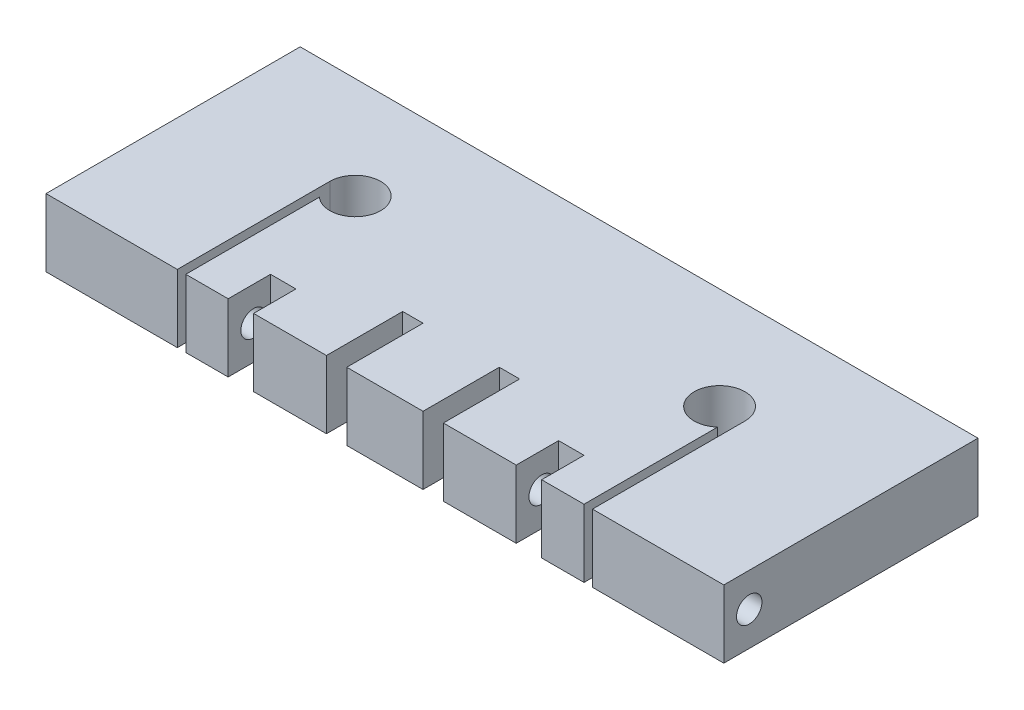
SolidWorks part; units mm, degrees
ref_plane "前视基准面" through (0, 0, 0) normal (0, 0, 1) x (1, 0, 0)
ref_plane "上视基准面" through (0, 0, 0) normal (0, 1, 0) x (1, 0, 0)
ref_plane "右视基准面" through (0, 0, 0) normal (1, 0, 0) x (0, 0, -1)
sketch "草图1" plane through (0, 0, 0) normal (0, 1, 0) x (1, 0, 0)
  line L1 (-40, -15) -> (40, -15)
  line L2 (-40, -15) -> (-40, 15)
  line L3 (-40, 15) -> (40, 15)
  line L4 (40, -15) -> (40, 15)
  line L5 (-40, -15) -> (40, 15) construction
  line L6 (-40, 15) -> (40, -15) construction
  point P0 (0, 0)
  dimension "D1" = 80
  dimension "D2" = 30
extrude "凸台-拉伸1" add sketch "草图1" along normal blind 8
sketch "草图2" plane through (0, 8, 0) normal (0, 1, 0) x (1, 0, 0)
  line L0 (0, 27.7349) -> (0, -22.8781) construction
  line L1 (-24.5, 3) -> (-24.5, -15)
  line L2 (-40, -15) -> (40, -15) construction
  line L3 (-24.5, -15) -> (-23.5, -15)
  line L4 (-23.5, -15) -> (-23.5, 0.7639)
  line L5 (23.5, -15) -> (23.5, 0.7639) construction
  line L6 (24.5, -15) -> (23.5, -15) construction
  line L7 (24.5, 3) -> (24.5, -15) construction
  line L8 (23.5, -15) -> (23.5, 0.7639)
  line L9 (24.5, -15) -> (23.5, -15)
  line L10 (24.5, 3) -> (24.5, -15)
  line L11 (40, 15) -> (-40, 15) construction
  arc A0 (-23.5, 0.7639) -> (-24.5, 3) centre (-21.5, 3) ccw
  arc A1 (23.5, 0.7639) -> (24.5, 3) centre (21.5, 3) cw construction
  arc A2 (-24.5, 3) -> (-23.5, 0.7639) centre (-21.5, 3) ccw construction
  arc A3 (23.5, 0.7639) -> (24.5, 3) centre (21.5, 3) cw construction
  arc A4 (24.5, 3) -> (23.5, 0.7639) centre (21.5, 3) cw construction
  arc A5 (23.5, 0.7639) -> (24.5, 3) centre (21.5, 3) cw
  dimension "D1" = 43
  dimension "D2" = 6
  dimension "D3" = 1
  dimension "D4" = 12
extrude "切除-拉伸1" cut sketch "草图2" against normal through all
sketch "草图3" plane through (0, 8, 0) normal (0, 1, 0) x (1, 0, 0)
  line L0 (0, 25.2639) -> (0, -30.4616) construction
  line L1 (-40, -15) -> (-24.5, -15) construction
  line L2 (-4.5, -15) -> (-6.9, -15)
  line L3 (-4.5, -15) -> (-4.5, -6)
  line L4 (-4.5, -6) -> (-6.9, -6)
  line L5 (-6.9, -15) -> (-6.9, -6)
  line L6 (4.5, -6) -> (6.9, -6)
  line L7 (6.9, -15) -> (6.9, -6)
  line L8 (4.5, -15) -> (6.9, -15)
  line L9 (4.5, -15) -> (4.5, -6)
  dimension "D1" = 9
  dimension "D2" = 2.4
  dimension "D3" = 9
extrude "切除-拉伸2" cut sketch "草图3" against normal through all and the other way through all
sketch "草图5" plane through (-40, 0, 0) normal (-1, 0, 0) x (0, 0, 1)
  line L0 (-15, 8) -> (15, 8) construction
  line L2 (15, 8) -> (15, 0) construction
  circle A0 centre (12, 4) radius 1.5
  dimension "D1" = 3
  dimension "D2" = 4
  dimension "D3" = 3
extrude "切除-拉伸3" cut sketch "草图5" against normal blind 32
sketch "草图6" plane through (0, 0, 15) normal (0, 0, 1) x (1, 0, 0)
  line L0 (-23.5, 8) -> (-6.9, 8) construction
  line L1 (-18.5, 8) -> (-15.5, 8)
  line L2 (-18.5, 8) -> (-18.5, 0)
  line L3 (-18.5, 0) -> (-15.5, 0)
  line L4 (-15.5, 8) -> (-15.5, 0)
  line L5 (-23.5, 0) -> (-6.9, 0) construction
  line L7 (0, 20.5142) -> (0, -11.4704) construction
  line L8 (18.5, 0) -> (15.5, 0)
  line L9 (15.5, 8) -> (15.5, 0)
  line L10 (18.5, 8) -> (15.5, 8)
  line L11 (18.5, 8) -> (18.5, 0)
  line L12 (-23.5, 0) -> (-23.5, 8) construction
  dimension "D1" = 5
  dimension "D2" = 3
extrude "切除-拉伸5" cut sketch "草图6" against normal blind 5
sketch "草图7" plane through (40, 0, 0) normal (1, 0, 0) x (0, 0, -1)
  line L0 (-15, 8) -> (15, 8) construction
  line L1 (-15, 8) -> (-15, 0) construction
  circle A0 centre (-12, 4) radius 1.5
  dimension "D1" = 3
  dimension "D2" = 4
  dimension "D3" = 3
extrude "切除-拉伸6" cut sketch "草图7" against normal blind 32
